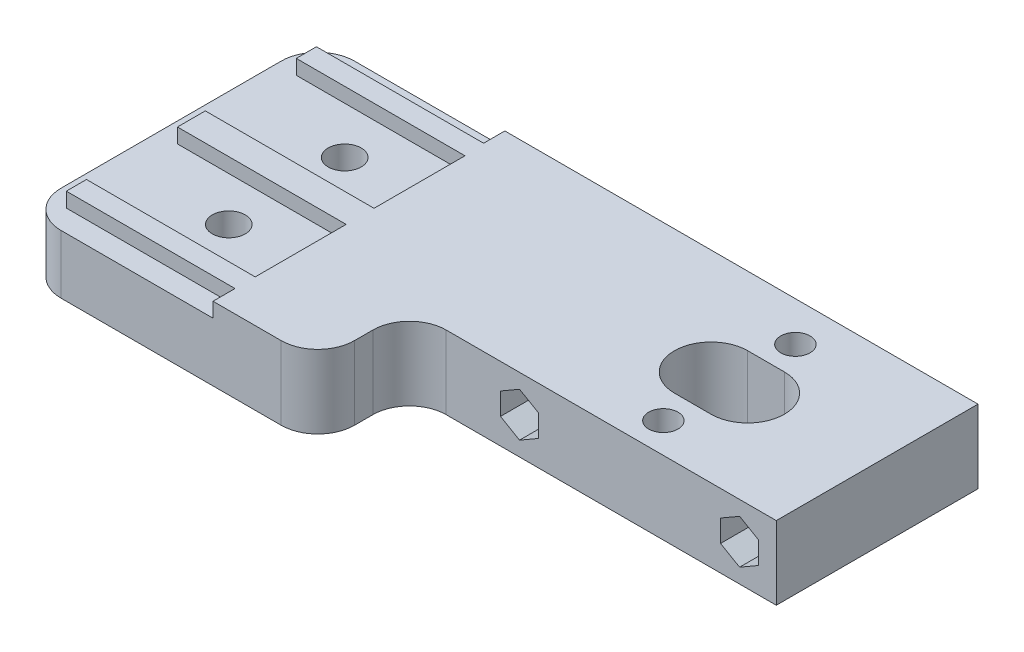
SolidWorks part; units mm, degrees
ref_plane "Front Plane" through (0, 0, 0) normal (0, 0, 1) x (1, 0, 0)
ref_plane "Top Plane" through (0, 0, 0) normal (0, 1, 0) x (1, 0, 0)
ref_plane "Right Plane" through (0, 0, 0) normal (1, 0, 0) x (0, 0, -1)
sketch "Sketch1" plane through (0, 0, 0) normal (0, 1, 0) x (1, 0, 0)
  line L1 (0, 0) -> (-90, 0)
  line L2 (0, 0) -> (0, 27.5)
  line L3 (0, 27.5) -> (-90, 27.5)
  line L4 (-90, 0) -> (-90, 27.5)
  dimension "D1" = 90
  dimension "D2" = 27.5
extrude "Boss-Extrude1" add sketch "Sketch1" along normal blind 10
sketch "Sketch2" plane through (0, 0, 0) normal (0, 0, 1) x (1, 0, 0)
  line L0 (-90, 10) -> (0, 10) construction
  line L1 (-32.4, 3.4989) -> (-32.4, 6.5011)
  line L2 (-32.4, 6.5011) -> (-35, 8.0022)
  line L3 (-35, 8.0022) -> (-37.6, 6.5011)
  line L4 (-37.6, 6.5011) -> (-37.6, 3.4989)
  line L5 (-37.6, 3.4989) -> (-35, 1.9978)
  line L6 (-35, 1.9978) -> (-32.4, 3.4989)
  line L7 (-2.4, 3.4989) -> (-2.4, 6.5011)
  line L8 (-2.4, 6.5011) -> (-5, 8.0022)
  line L9 (-5, 8.0022) -> (-7.6, 6.5011)
  line L10 (-7.6, 6.5011) -> (-7.6, 3.4989)
  line L11 (-7.6, 3.4989) -> (-5, 1.9978)
  line L12 (-5, 1.9978) -> (-2.4, 3.4989)
  line L13 (0, 10) -> (0, 0) construction
  circle A0 centre (-35, 5) radius 2.6 construction
  circle A1 centre (-5, 5) radius 2.6 construction
  dimension "D5" = 5.2
  dimension "D6" = 5.2
  dimension "D1" = 5
  dimension "D2" = 0
  dimension "D3" = 5
  dimension "D4" = 0
  dimension "D7" = 30
  dimension "D8" = 5
extrude "Cut-Extrude1" cut sketch "Sketch2" against normal through all
sketch "Sketch9" plane through (0, 10, 0) normal (0, 1, 0) x (1, 0, 0)
  line L1 (-90, 27.5) -> (-50, 27.5)
  line L2 (-90, 27.5) -> (-90, -12.5)
  line L3 (-90, -12.5) -> (-50, -12.5)
  line L4 (-50, 27.5) -> (-50, -12.5)
  dimension "D1" = 40
  dimension "D2" = 40
extrude "Boss-Extrude3" add sketch "Sketch9" against normal up to surface (10 mm away) up to face at (-45, 0, -13.75)
sketch "Sketch4" plane through (-50, 10, 0) normal (0, 1, 0) x (0, 0, -1)
  line L0 (27.6, 44.8411) -> (27.6, 37.2586)
  line L10 (-6.75, 30.4892) -> (-6.75, 14.2892)
  line L11 (-6.75, 14.2892) -> (5.65, 14.2892)
  line L12 (5.65, 30.4892) -> (5.65, 14.2892)
  line L14 (9.45, 30.4892) -> (9.45, 14.2892)
  line L15 (9.45, 14.2892) -> (21.85, 14.2892)
  line L16 (21.85, 30.4892) -> (21.85, 14.2892)
  line L17 (-9.5, 14.2892) -> (-12.5, 14.2892)
  line L18 (-9.5, 14.2892) -> (-9.5, 37.2892)
  line L20 (-12.5, 14.2892) -> (-12.5, 37.2892)
  line L21 (24.6, 14.5043) -> (27.6, 14.5043)
  line L22 (24.6, 14.5043) -> (24.6, 37.2892)
  line L24 (27.6, 14.5043) -> (27.6, 37.2586)
  line L25 (-9.5, 37.2892) -> (-6.75, 37.2892)
  line L26 (-12.5, 37.2892) -> (-12.5, 44.8411)
  line L27 (-12.5, 44.8411) -> (27.6, 44.8411)
  line L28 (-12.5, 40) -> (-12.5, 0) construction
  line L29 (-6.75, 30.4892) -> (-6.75, 37.2892)
  line L30 (5.65, 30.4892) -> (5.65, 37.2892)
  line L31 (9.45, 30.4892) -> (9.45, 37.2892)
  line L32 (21.85, 30.4892) -> (21.85, 37.2892)
  line L33 (5.65, 37.2892) -> (9.45, 37.2892)
  line L34 (21.85, 37.2892) -> (24.6, 37.2892)
  dimension "D1" = 12.4
  dimension "D2" = 12.4
  dimension "D3" = 23
  dimension "D4" = 23
  dimension "D5" = 3.8
  dimension "D7" = 2.75
  dimension "D8" = 2.75
  dimension "D9" = 3
  dimension "D10" = 3
  dimension "D11" = 23
  dimension "D13" = 0
extrude "Cut-Extrude2" cut sketch "Sketch4" against normal blind 2
hole_wizard "M4 Clearance Hole1" positions "Sketch5" profile "Sketch7" hole size "M4" standard "ANSI Metric" end condition through all
sketch "Sketch5" plane through (0, 8, 0) normal (0, 1, 0) x (0, 0, -1)
  line L0 (5.65, 64.2892) -> (5.65, 87.2892) construction
  line L1 (9.45, 87.2892) -> (9.45, 64.2892) construction
  line L4 (-6.75, 64.2892) -> (5.65, 64.2892) construction
  line L5 (9.45, 64.2892) -> (21.85, 64.2892) construction
  point P0 (-0.35, 74.2892)
  point P2 (15.45, 74.2892)
  dimension "D1" = 6
  dimension "D2" = 6
  dimension "D3" = 10
  dimension "D4" = 10
sketch "Sketch7" plane through (-74.2892, 8, 0.35) normal (1, 0, 0) x (0, 0, 1)
  line L0 (0, 0) -> (0, 8)
  line L1 (0, 8) -> (2.25, 8)
  line L2 (2.25, 8) -> (2.25, 0)
  line L5 (2.25, 0) -> (0, 0)
  line L11 (0, -6.35) -> (0, 107.95) construction
  dimension "Thru Hole Dia." = 4.5
  dimension "Thru Hole Depth" = 8
fillet "Fillet1" radius 5 4 edges at (-90, 4, -27.5) (-90, 4, 12.5) (-50, 5, 12.5) (-50, 5, 0)
sketch "Sketch10" plane through (0, 10, 0) normal (0, 1, 0) x (1, 0, 0)
  line L0 (-17, 13.1062) -> (-22, 13.1062) construction
  line L1 (-17, 8.1062) -> (-22, 8.1062)
  line L2 (-17, 18.1062) -> (-22, 18.1062)
  line L3 (0, 0) -> (0, 27.5) construction
  arc A0 (-17, 8.1062) -> (-17, 18.1062) centre (-17, 13.1062) ccw
  arc A1 (-22, 18.1062) -> (-22, 8.1062) centre (-22, 13.1062) ccw
  circle A2 centre (-19.5, 4.1062) radius 2
  circle A3 centre (-19.5, 22.1062) radius 2
  point P2 (-19.5, 13.1062)
  dimension "D3" = 5
  dimension "D4" = 4
  dimension "D5" = 4
  dimension "D1" = 5
  dimension "D2" = 17
  dimension "D6" = 9
  dimension "D7" = 9
extrude "Cut-Extrude3" cut sketch "Sketch10" against normal through all
